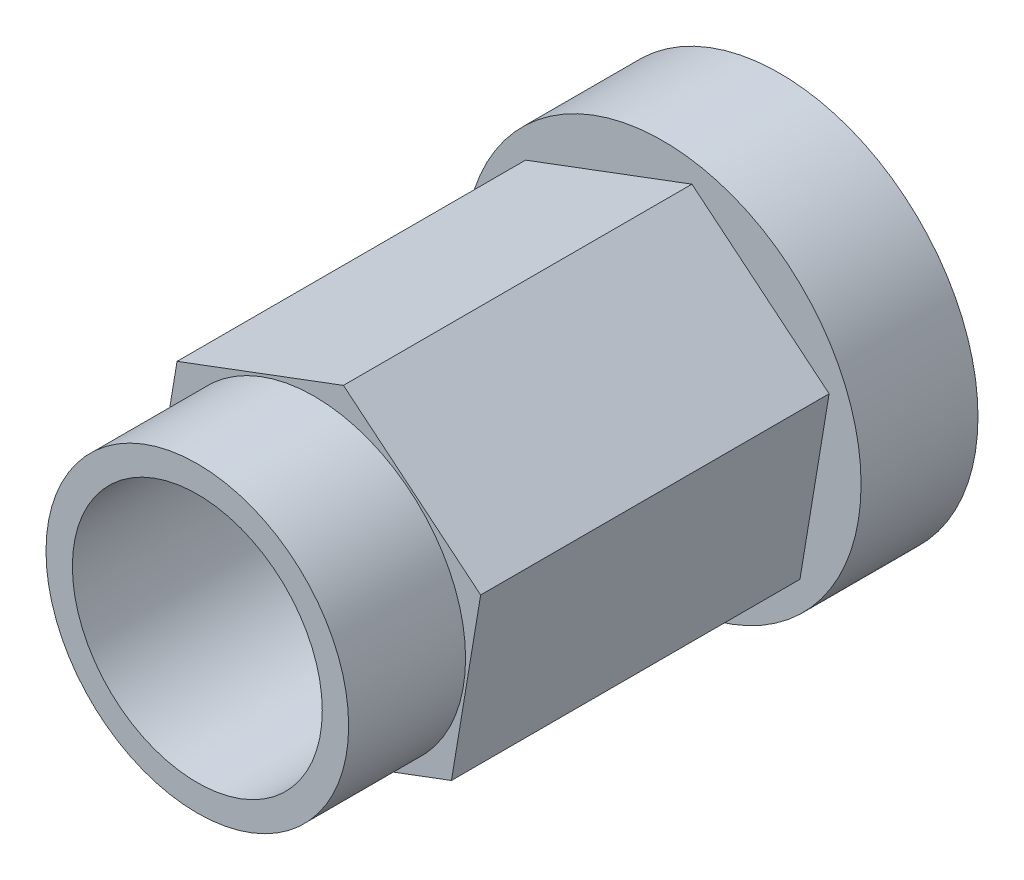
SolidWorks part; units mm, degrees
ref_plane "Front Plane" through (0, 0, 0) normal (0, 0, 1) x (1, 0, 0)
ref_plane "Top Plane" through (0, 0, 0) normal (0, 1, 0) x (1, 0, 0)
ref_plane "Right Plane" through (0, 0, 0) normal (1, 0, 0) x (0, 0, -1)
sketch "Sketch1" plane through (0, 0, 0) normal (0, 0, 1) x (1, 0, 0)
  line L3 (-0.7257, -0.272) -> (-0.1273, -0.7645)
  line L4 (-0.1273, -0.7645) -> (0.5984, -0.4925)
  line L5 (0.5984, -0.4925) -> (0.7257, 0.272)
  line L6 (0.7257, 0.272) -> (0.1273, 0.7645)
  line L7 (0.1273, 0.7645) -> (-0.5984, 0.4925)
  line L8 (-0.5984, 0.4925) -> (-0.7257, -0.272)
  circle A0 centre (0, 0) radius 0.775 construction
extrude "Boss-Extrude1" add sketch "Sketch1" along normal blind 1.52
sketch "Sketch4" plane through (0, 0, 1.52) normal (0, 0, 1) x (1, 0, 0)
  circle A0 centre (0, 0) radius 0.66
extrude "Boss-Extrude3" add sketch "Sketch4" along normal blind 0.51
sketch "Sketch2" plane through (0, 0, 0) normal (0, 0, -1) x (-1, 0, 0)
  circle A0 centre (0, 0) radius 0.865
extrude "Boss-Extrude2" add sketch "Sketch2" along normal blind 0.51
sketch "Sketch3" plane through (0, 0, -0.51) normal (0, 0, -1) x (-1, 0, 0)
  circle A0 centre (0, 0) radius 0.545
extrude "Cut-Extrude1" cut sketch "Sketch3" against normal blind 2.54
